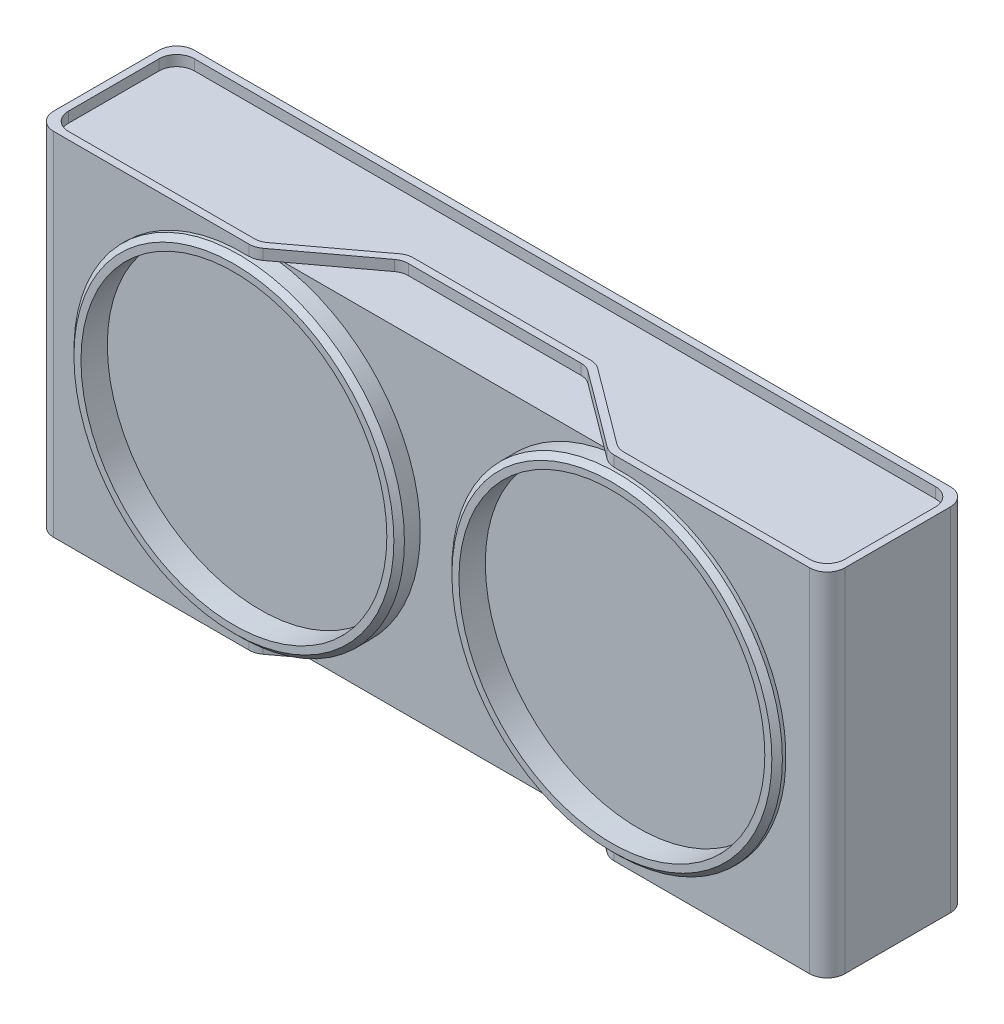
SolidWorks part; units mm, degrees
ref_plane "Front Plane" through (0, 0, 0) normal (0, 0, 1) x (1, 0, 0)
ref_plane "Top Plane" through (0, 0, 0) normal (0, 1, 0) x (1, 0, 0)
ref_plane "Right Plane" through (0, 0, 0) normal (1, 0, 0) x (0, 0, -1)
sketch "Sketch1" plane through (0, 0, 0) normal (0, 0, 1) x (1, 0, 0)
  line L1 (0, 0) -> (45, 0)
  line L2 (0, 0) -> (0, 20)
  line L3 (0, 20) -> (45, 20)
  line L4 (45, 0) -> (45, 20)
  dimension "D1" = 20
  dimension "D2" = 45
extrude "Boss-Extrude1" add sketch "Sketch1" along normal blind 8
fillet "Fillet1" radius 1 4 edges at (45, 10, 8) (0, 10, 8) (45, 10, 0) (0, 10, 0)
sketch "Sketch3" plane through (0, 0, 8) normal (0, 0, 1) x (1, 0, 0)
  line L0 (1, 10) -> (44, 10) construction
  line L1 (1, 20) -> (1, 0) construction
  line L2 (44, 0) -> (44, 20) construction
  line L3 (22.5, 20) -> (22.5, 0) construction
  line L4 (44, 20) -> (1, 20) construction
  line L5 (1, 0) -> (44, 0) construction
  line L6 (22.5, 10) -> (1, 10) construction
  line L7 (22.5, 10) -> (44, 10) construction
  circle A0 centre (11.75, 10) radius 9.4
  circle A1 centre (33.25, 10) radius 9.4
  circle A2 centre (11.75, 10) radius 8.7
  circle A3 centre (33.25, 10) radius 8.7
  dimension "D1" = 18.8
  dimension "D2" = 18.8
  dimension "D3" = 0.7
  dimension "D4" = 0.7
extrude "Boss-Extrude2" add sketch "Sketch3" along normal blind 0.5
sketch "Sketch4" plane through (0, 0, 0) normal (0, -1, 0) x (1, 0, 0)
  line L0 (22.5, 8) -> (22.5, 0) construction
  line L1 (1, 8) -> (44, 8) construction
  line L2 (1, 0) -> (44, 0) construction
  line L3 (11.75, 8.5) -> (11.75, 0) construction
  line L4 (20.45, 8.5) -> (3.05, 8.5) construction
  line L5 (33.25, 8.5) -> (33.25, 0) construction
  line L6 (41.95, 8.5) -> (24.55, 8.5) construction
  line L7 (22.5, 4) -> (11.75, 4) construction
  line L8 (11.75, 4) -> (33.25, 4) construction
  line L9 (11.75, 8) -> (17.125, 4) construction
  line L10 (33.25, 4) -> (22.5, 4) construction
  line L11 (33.25, 8) -> (27.875, 4) construction
  line L12 (27.875, 4) -> (17.125, 4) construction
  line L13 (33.25, 8) -> (27.875, 4)
  line L14 (27.875, 4) -> (17.125, 4)
  line L15 (17.125, 4) -> (11.75, 8)
  line L16 (11.75, 8) -> (17.125, 4)
  line L17 (11.75, 8) -> (12.45, 8)
  line L18 (17.125, 4) -> (17.825, 4)
  line L19 (12.45, 8) -> (17.825, 4)
  line L20 (33.25, 8) -> (27.875, 4)
  line L21 (33.25, 8) -> (32.55, 8)
  line L22 (27.875, 4) -> (27.175, 4)
  line L23 (32.55, 8) -> (27.175, 4)
  line L24 (12.45, 8) -> (32.55, 8)
  line L25 (17.125, 4) -> (27.875, 4)
  line L26 (17.125, 4) -> (17.125, 4.42)
  line L27 (17.125, 4.42) -> (27.875, 4.42)
  line L28 (27.875, 4) -> (27.875, 4.42)
  line L30 (32.55, 8) -> (45, 8)
  line L31 (32.55, 8) -> (32.55, 7.58)
  line L32 (32.55, 7.58) -> (45, 7.58)
  line L33 (45, 8) -> (45, 7.58)
  line L34 (45, 7.58) -> (44.58, 7.58)
  line L35 (45, 7.58) -> (45, 0)
  line L36 (45, 0) -> (44.58, 0)
  line L37 (44.58, 7.58) -> (44.58, 0)
  line L38 (45, 0) -> (0, 0)
  line L39 (45, 0) -> (45, 0.42)
  line L40 (45, 0.42) -> (0, 0.42)
  line L41 (0, 0) -> (0, 0.42)
  line L42 (12.45, 8) -> (0, 8)
  line L43 (12.45, 8) -> (12.45, 7.58)
  line L44 (12.45, 7.58) -> (0, 7.58)
  line L45 (0, 8) -> (0, 7.58)
  line L46 (0, 8) -> (0.42, 8)
  line L47 (0, 8) -> (0, 0)
  line L48 (0, 0) -> (0.42, 0)
  line L49 (0.42, 8) -> (0.42, 0)
  line M6 (44, 8) -> (1, 8)
  dimension "D1" = 0.7
  dimension "D2" = 0.7
  dimension "D3" = 0.42
  dimension "D4" = 0.42
  dimension "D5" = 0.42
  dimension "D6" = 0.42
  dimension "D7" = 0.42
  dimension "D8" = 0.42
extrude "Cut-Extrude1" cut sketch "Sketch4" against normal blind 0.6 contours L19 L27 L23 M6 | L44 L49 L40 L37 L32 L20 L14 L15
fillet "Fillet2" radius 1 12 edges at (44.58, 0.3, 0.42) (44.58, 0.3, 7.58) (32.6856, 0.3, 7.58) (32.55, 0.3, 8) (27.7394, 0.3, 4.42) (27.875, 0.3, 4) (17.2606, 0.3, 4.42) (17.125, 0.3, 4) (12.3144, 0.3, 7.58) (12.45, 0.3, 8) (0.42, 0.3, 7.58) (0.42, 0.3, 0.42)
pattern_linear "LPattern3" count 2 spacing 19.4 along (0, 1, 0) of "Cut-Extrude1", "Fillet2"
sketch "Sketch6" plane through (0, 0, 8) normal (0, 0, 1) x (1, 0, 0)
  line L1 (12.1187, 19.4) -> (32.8813, 19.4)
  line L2 (12.1187, 19.4) -> (12.1187, 0.6)
  line L3 (12.1187, 0.6) -> (32.8813, 0.6)
  line L4 (32.8813, 19.4) -> (32.8813, 0.6)
extrude "Cut-Extrude3" cut sketch "Sketch6" against normal blind 0.7
sketch "Sketch7" plane through (0, 0, 8.5) normal (0, 0, 1) x (1, 0, 0)
  circle A0 centre (11.75, 10) radius 8.7
  circle A1 centre (11.75, 10) radius 9.4
extrude "Boss-Extrude4" add sketch "Sketch7" against normal blind 1.3
sketch "Sketch8" plane through (0, 0, 8.5) normal (0, 0, 1) x (1, 0, 0)
  circle A0 centre (33.25, 10) radius 8.7
  circle A1 centre (33.25, 10) radius 9.4
extrude "Boss-Extrude5" add sketch "Sketch8" against normal blind 1.3
chamfer "Chamfer1" distance 0.3 angle 45 2 edges at (42.65, 10, 8.5) (21.15, 10, 8.5)
sketch "Sketch12" plane through (0, 0, 8) normal (0, 0, 1) x (1, 0, 0)
  circle A0 centre (33.25, 10) radius 8.7
extrude "Cut-Extrude4" cut sketch "Sketch12" against normal blind 1
sketch "Sketch13" plane through (0, 0, 8) normal (0, 0, 1) x (1, 0, 0)
  circle A0 centre (11.75, 10) radius 8.7
extrude "Cut-Extrude5" cut sketch "Sketch13" against normal blind 1
sketch "Sketch14" plane through (0, 0, 7) normal (0, 0, 1) x (1, 0, 0)
  circle A0 centre (11.75, 10) radius 3.85
  circle A1 centre (33.25, 10) radius 3.85
  dimension "D1" = 7.7
  dimension "D2" = 7.7
sketch "Sketch19" plane through (0, 0, 0) normal (-1, 0, 0) x (0, 0, 1)
  line L0 (4, 20) -> (4, 0) construction
  line L1 (7, 20) -> (1, 20) construction
  line L2 (7, 10) -> (1, 10) construction
  line L3 (7, 0) -> (7, 20) construction
  line L4 (1, 20) -> (1, 0) construction
  line L6 (1.5, 16.5) -> (6.5, 16.5)
  line L7 (1.5, 16.5) -> (1.5, 3.5)
  line L8 (1.5, 3.5) -> (6.5, 3.5)
  line L9 (6.5, 16.5) -> (6.5, 3.5)
  line L10 (1.5, 16.5) -> (6.5, 3.5) construction
  line L11 (1.5, 3.5) -> (6.5, 16.5) construction
  line L12 (3, 2.5) -> (5, 2.5)
  line L13 (3, 2.5) -> (3, 17.5)
  line L14 (3, 17.5) -> (5, 17.5)
  line L15 (5, 2.5) -> (5, 17.5)
  line L16 (3, 2.5) -> (5, 17.5) construction
  line L17 (3, 17.5) -> (5, 2.5) construction
  point P11 (4, 10)
  point P16 (4, 10)
  dimension "D1" = 13
  dimension "D2" = 5
  dimension "D3" = 15
  dimension "D4" = 2
extrude "Cut-Extrude6" cut sketch "Sketch19" against normal blind 40 contours L15 L8 L9 L6 | L8 L15 L6 L13 | L6 L15 L14 L13 | L12 L15 L8 L13 | L8 L13 L6 L7
